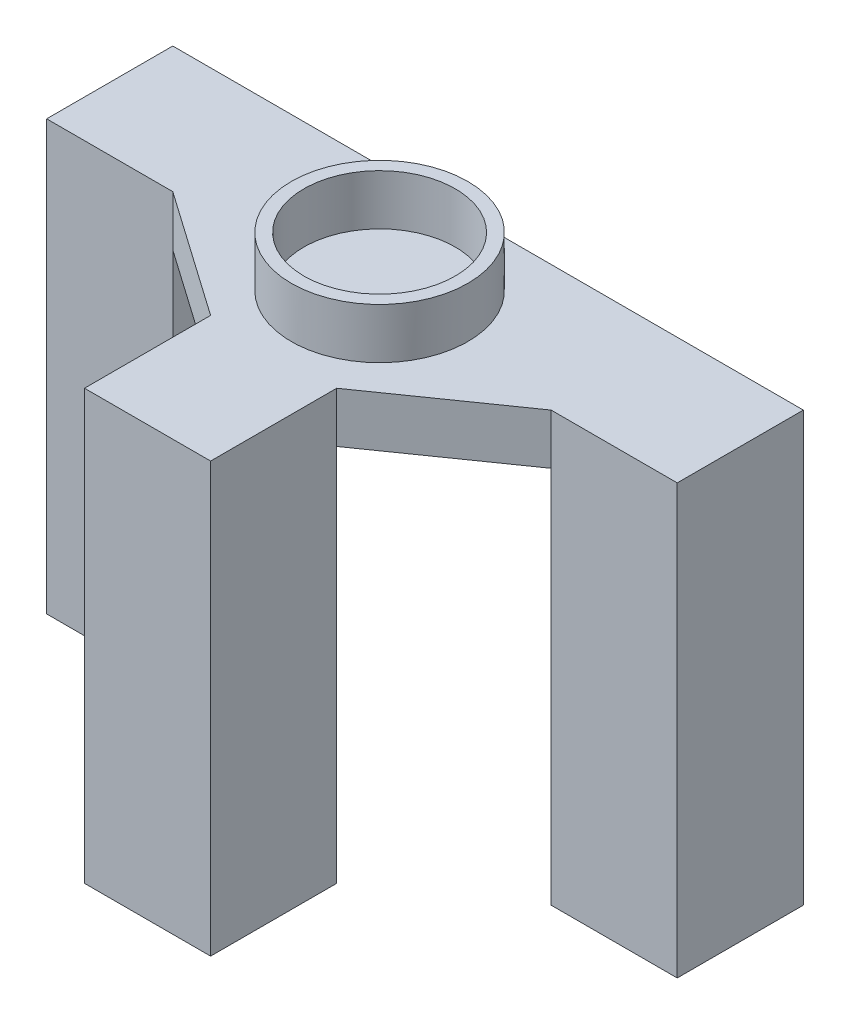
SolidWorks part; units mm, degrees
ref_plane "Front" through (0, 0, 0) normal (0, 0, 1) x (1, 0, 0)
ref_plane "Top" through (0, 0, 0) normal (0, 1, 0) x (1, 0, 0)
ref_plane "Right" through (0, 0, 0) normal (1, 0, 0) x (0, 0, -1)
sketch "草图1" plane through (0, 0, 0) normal (0, 1, 0) x (1, 0, 0)
  line L0 (-31.9558, 0) -> (0, 0) construction
  line L1 (-25, 5) -> (-15, 5)
  line L2 (-25, 5) -> (-25, -5)
  line L3 (-25, -5) -> (-15, -5)
  line L4 (-15, 5) -> (-15, -5)
  line L5 (15, 5) -> (25, 5)
  line L6 (15, 5) -> (15, -5)
  line L7 (15, -5) -> (25, -5)
  line L8 (25, 5) -> (25, -5)
  line L9 (-5, -12) -> (5, -12) construction
  line L10 (-5, -12) -> (-5, -22) construction
  line L11 (-5, -22) -> (5, -22) construction
  line L12 (5, -12) -> (5, -22) construction
  line L13 (0, 0) -> (0, 15.9462) construction
  dimension "D1" = 10
  dimension "D2" = 10
  dimension "D3" = 10
  dimension "D4" = 10
  dimension "D5" = 5
  dimension "D6" = 5
  dimension "D7" = 10
  dimension "D8" = 10
  dimension "D9" = 5
  dimension "D10" = 15
  dimension "D11" = 15
  dimension "D12" = 12
sketch "草图2" plane through (0, 0, 0) normal (0, 1, 0) x (1, 0, 0)
  line L0 (-25, -5) -> (-25, 23.5912) construction
  line L1 (25, -5) -> (25, 17.5149) construction
  line L2 (-25, 5) -> (25, 5) construction
  line L12 (-5, -22) -> (5, -22)
  line L19 (25, -5) -> (25, 5)
  line L20 (25, 5) -> (-25, 5)
  line L21 (-25, 5) -> (-25, -5)
  line L22 (-25, -5) -> (-15, -5)
  line L23 (-15, -5) -> (-5, -12)
  line L24 (-5, -12) -> (-5, -22)
  line L25 (5, -22) -> (5, -12)
  line L26 (5, -12) -> (15, -5)
  line L27 (15, -5) -> (25, -5)
extrude "凸台-拉伸1" add sketch "草图2" along normal blind 4
extrude "凸台-拉伸2" add sketch "草图1" against normal blind 30
sketch "草图6" plane through (0, 0, 0) normal (0, -1, 0) x (1, 0, 0)
  line L1 (-5, 22) -> (5, 22)
  line L2 (-5, 22) -> (-5, 12)
  line L3 (-5, 12) -> (5, 12)
  line L4 (5, 22) -> (5, 12)
extrude "凸台-拉伸4" add sketch "草图6" along normal blind 30
sketch "草图9" plane through (0, 4, 0) normal (0, 1, 0) x (1, 0, 0)
  circle A0 centre (0, -3.6) radius 6
  circle A1 centre (0, -3.6) radius 7
extrude "凸台-拉伸5" add sketch "草图9" along normal blind 4
sketch "草图11" plane through (0, -30, 0) normal (0, -1, 0) x (1, 0, 0)
  circle A0 centre (0, 17) radius 4
  circle A1 centre (20, 0) radius 4
  circle A2 centre (-20, 0) radius 4
extrude "切除-拉伸1" cut sketch "草图11" against normal blind 30
